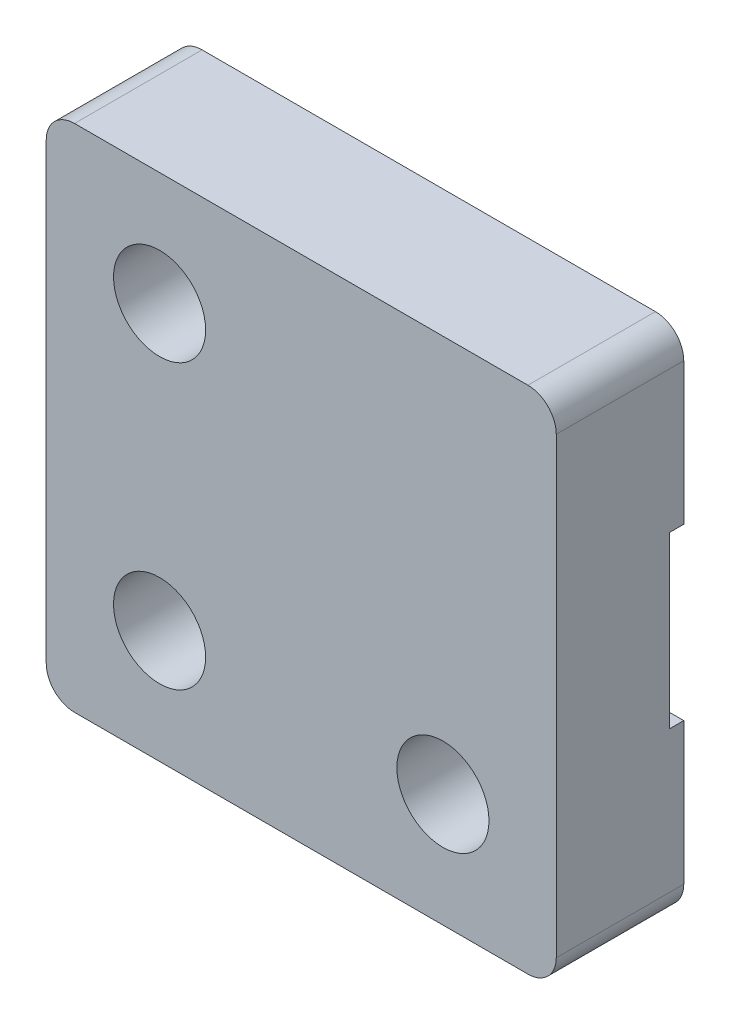
SolidWorks part; units mm, degrees
ref_plane "Front Plane" through (0, 0, 0) normal (0, 0, 1) x (1, 0, 0)
ref_plane "Top Plane" through (0, 0, 0) normal (0, 1, 0) x (1, 0, 0)
ref_plane "Right Plane" through (0, 0, 0) normal (1, 0, 0) x (0, 0, -1)
sketch "Sketch1" plane through (0, 0, 0) normal (0, 0, 1) x (1, 0, 0)
  line L0 (14, 14) -> (14, 4) construction
  line L1 (0, 0) -> (18, 0)
  line L2 (0, 0) -> (0, 18)
  line L3 (0, 18) -> (18, 18)
  line L4 (18, 0) -> (18, 18)
  line L5 (14, 4) -> (4, 4) construction
  circle A0 centre (4, 4) radius 1.625
  circle A1 centre (14, 4) radius 1.625
  circle A2 centre (14, 14) radius 1.625
  dimension "D1" = 3.25
  dimension "D2" = 18
  dimension "D3" = 10
  dimension "D4" = 4
  dimension "D5" = 4
extrude "Boss-Extrude1" add sketch "Sketch1" along normal blind 4
sketch "Sketch2" plane through (0, 0, 0) normal (0, 0, -1) x (-1, 0, 0)
  line L0 (-18, 0) -> (-18, 18) construction
  line L1 (-18, 12) -> (-17, 12)
  line L2 (-18, 12) -> (-18, 6)
  line L3 (-18, 6) -> (-17, 6)
  line L4 (-17, 12) -> (-17, 6)
  line L5 (-16, 12) -> (-16, 6)
  line L6 (-17, 12) -> (-16, 12)
  line L7 (-17, 12) -> (-17, 6)
  line L8 (-17, 6) -> (-16, 6)
  line L9 (-15, 12) -> (-15, 6)
  line L10 (-16, 12) -> (-15, 12)
  line L11 (-16, 12) -> (-16, 6)
  line L12 (-16, 6) -> (-15, 6)
  line L13 (-14, 12) -> (-14, 6)
  line L14 (-15, 12) -> (-14, 12)
  line L15 (-15, 12) -> (-15, 6)
  line L16 (-15, 6) -> (-14, 6)
  line L17 (-13, 12) -> (-13, 6)
  line L18 (-14, 12) -> (-13, 12)
  line L19 (-14, 12) -> (-14, 6)
  line L20 (-14, 6) -> (-13, 6)
  line L21 (-12, 12) -> (-12, 6)
  line L22 (-13, 12) -> (-12, 12)
  line L23 (-13, 12) -> (-13, 6)
  line L24 (-13, 6) -> (-12, 6)
  line L25 (-11, 12) -> (-11, 6)
  line L26 (-12, 12) -> (-11, 12)
  line L27 (-12, 12) -> (-12, 6)
  line L28 (-12, 6) -> (-11, 6)
  line L29 (-10, 12) -> (-10, 6)
  line L30 (-11, 12) -> (-10, 12)
  line L31 (-11, 12) -> (-11, 6)
  line L32 (-11, 6) -> (-10, 6)
  line L33 (-9, 12) -> (-9, 6)
  line L34 (-10, 12) -> (-9, 12)
  line L35 (-10, 12) -> (-10, 6)
  line L36 (-10, 6) -> (-9, 6)
  line L37 (-8, 12) -> (-8, 6)
  line L38 (-9, 12) -> (-8, 12)
  line L39 (-9, 12) -> (-9, 6)
  line L40 (-9, 6) -> (-8, 6)
  line L41 (-7, 12) -> (-7, 6)
  line L42 (-8, 12) -> (-7, 12)
  line L43 (-8, 12) -> (-8, 6)
  line L44 (-8, 6) -> (-7, 6)
  line L45 (-6, 12) -> (-6, 6)
  line L46 (-7, 12) -> (-6, 12)
  line L47 (-7, 12) -> (-7, 6)
  line L48 (-7, 6) -> (-6, 6)
  line L49 (-5, 12) -> (-5, 6)
  line L50 (-6, 12) -> (-5, 12)
  line L51 (-6, 12) -> (-6, 6)
  line L52 (-6, 6) -> (-5, 6)
  line L53 (-4, 12) -> (-4, 6)
  line L54 (-5, 12) -> (-4, 12)
  line L55 (-5, 12) -> (-5, 6)
  line L56 (-5, 6) -> (-4, 6)
  line L57 (-3, 12) -> (-3, 6)
  line L58 (-4, 12) -> (-3, 12)
  line L59 (-4, 12) -> (-4, 6)
  line L60 (-4, 6) -> (-3, 6)
  line L61 (-2, 12) -> (-2, 6)
  line L62 (-3, 12) -> (-2, 12)
  line L63 (-3, 12) -> (-3, 6)
  line L64 (-3, 6) -> (-2, 6)
  line L65 (-1, 12) -> (-1, 6)
  line L66 (-2, 12) -> (-1, 12)
  line L67 (-2, 12) -> (-2, 6)
  line L68 (-2, 6) -> (-1, 6)
  line L69 (0, 12) -> (0, 6)
  line L70 (-1, 12) -> (0, 12)
  line L71 (-1, 12) -> (-1, 6)
  line L72 (-1, 6) -> (0, 6)
  line M7 (-18, 18) -> (-18, 0)
  dimension "D1" = 6
  dimension "D2" = 1
  dimension "D3" = 6
  dimension "D4" = 18
extrude "Cut-Extrude1" cut sketch "Sketch2" against normal blind 0.95 contours L4 L1 L3 M7 | L5 L12 L9 L10 | L13 L20 L17 L18 | L21 L28 L25 L26 | L29 L36 L33 L34 | L37 L44 L41 L42 | L45 L52 L49 L50 | L53 L60 L57 L58 | L61 L68 L65 L66
sketch "Sketch3" plane through (0, 0, 0) normal (0, 0, -1) x (-1, 0, 0)
  line L0 (0, 18) -> (0, 0) construction
  line L1 (-18, 18) -> (0, 18)
  line L2 (-18, 18) -> (-18, 12)
  line L3 (-18, 12) -> (0, 12)
  line L4 (-2, 12) -> (-2, 6)
  line L5 (-1, 12) -> (-2, 12)
  line L6 (-1, 6) -> (-1, 12)
  line L7 (-2, 6) -> (-1, 6)
  line L8 (-2, 12) -> (-2, 6)
  line L9 (-1, 12) -> (-2, 12)
  line L10 (-1, 6) -> (-1, 12)
  line L11 (-2, 6) -> (-1, 6)
  line L12 (-4, 12) -> (-4, 6)
  line L13 (-3, 12) -> (-4, 12)
  line L14 (-3, 6) -> (-3, 12)
  line L15 (-4, 6) -> (-3, 6)
  line L16 (-4, 12) -> (-4, 6)
  line L17 (-3, 12) -> (-4, 12)
  line L18 (-3, 6) -> (-3, 12)
  line L19 (-4, 6) -> (-3, 6)
  line L20 (-6, 12) -> (-6, 6)
  line L21 (-5, 12) -> (-6, 12)
  line L22 (-5, 6) -> (-5, 12)
  line L23 (-6, 6) -> (-5, 6)
  line L24 (-6, 12) -> (-6, 6)
  line L25 (-5, 12) -> (-6, 12)
  line L26 (-5, 6) -> (-5, 12)
  line L27 (-6, 6) -> (-5, 6)
  line L28 (-8, 12) -> (-8, 6)
  line L29 (-7, 12) -> (-8, 12)
  line L30 (-7, 6) -> (-7, 12)
  line L31 (-8, 6) -> (-7, 6)
  line L32 (-8, 12) -> (-8, 6)
  line L33 (-7, 12) -> (-8, 12)
  line L34 (-7, 6) -> (-7, 12)
  line L35 (-8, 6) -> (-7, 6)
  line L36 (-10, 12) -> (-10, 6)
  line L37 (-9, 12) -> (-10, 12)
  line L38 (-9, 6) -> (-9, 12)
  line L39 (-10, 6) -> (-9, 6)
  line L40 (-10, 12) -> (-10, 6)
  line L41 (-9, 12) -> (-10, 12)
  line L42 (-9, 6) -> (-9, 12)
  line L43 (-10, 6) -> (-9, 6)
  line L44 (-12, 12) -> (-12, 6)
  line L45 (-11, 12) -> (-12, 12)
  line L46 (-11, 6) -> (-11, 12)
  line L47 (-12, 6) -> (-11, 6)
  line L48 (-12, 12) -> (-12, 6)
  line L49 (-11, 12) -> (-12, 12)
  line L50 (-11, 6) -> (-11, 12)
  line L51 (-12, 6) -> (-11, 6)
  line L52 (-14, 12) -> (-14, 6)
  line L53 (-13, 12) -> (-14, 12)
  line L54 (-13, 6) -> (-13, 12)
  line L55 (-14, 6) -> (-13, 6)
  line L56 (-14, 12) -> (-14, 6)
  line L57 (-13, 12) -> (-14, 12)
  line L58 (-13, 6) -> (-13, 12)
  line L59 (-14, 6) -> (-13, 6)
  line L60 (-16, 12) -> (-16, 6)
  line L61 (-15, 12) -> (-16, 12)
  line L62 (-15, 6) -> (-15, 12)
  line L63 (-16, 6) -> (-15, 6)
  line L64 (-16, 12) -> (-16, 6)
  line L65 (-15, 12) -> (-16, 12)
  line L66 (-15, 6) -> (-15, 12)
  line L67 (-16, 6) -> (-15, 6)
  line L68 (0, 18) -> (0, 12)
  line L70 (-18, 6) -> (0, 6)
  line L71 (-18, 6) -> (-18, 0)
  line L72 (-18, 0) -> (0, 0)
  line L73 (0, 6) -> (0, 0)
  circle A1 centre (-4, 4) radius 1.625
  circle A2 centre (-4, 4) radius 1.625
  circle A3 centre (-14, 4) radius 1.625
  circle A4 centre (-14, 4) radius 1.625
  circle A5 centre (-14, 14) radius 1.625
  circle A6 centre (-14, 14) radius 1.625
  line M36 (-17, 6) -> (-18, 6)
  line M37 (-18, 6) -> (-18, 0)
  line M38 (-18, 0) -> (0, 0)
  line M39 (0, 0) -> (0, 18)
  line M40 (0, 18) -> (-18, 18)
  line M41 (-18, 18) -> (-18, 12)
  line M42 (-18, 12) -> (-17, 12)
  line M45 (-16, 12) -> (-15, 12)
  line M47 (-15, 6) -> (-16, 6)
  line M49 (-14, 12) -> (-13, 12)
  line M51 (-13, 6) -> (-14, 6)
  line M53 (-12, 12) -> (-11, 12)
  line M55 (-11, 6) -> (-12, 6)
  line M57 (-10, 12) -> (-9, 12)
  line M59 (-9, 6) -> (-10, 6)
  line M61 (-8, 12) -> (-7, 12)
  line M63 (-7, 6) -> (-8, 6)
  line M65 (-6, 12) -> (-5, 12)
  line M67 (-5, 6) -> (-6, 6)
  line M69 (-4, 12) -> (-3, 12)
  line M71 (-3, 6) -> (-4, 6)
  line M73 (-2, 12) -> (-1, 12)
  line M75 (-1, 6) -> (-2, 6)
  circle M76 centre (-14, 4) radius 1.625
  circle M77 centre (-4, 4) radius 1.625
  circle M78 centre (-14, 14) radius 1.625
  dimension "D1" = 0
  dimension "D2" = 0
  dimension "D3" = 0
  dimension "D4" = 0
  dimension "D5" = 0
  dimension "D6" = 0
  dimension "D7" = 0
  dimension "D8" = 0
  dimension "D9" = 0
  dimension "D10" = 0
  dimension "D11" = 0
extrude "Boss-Extrude2" add sketch "Sketch3" along normal blind 0.5 contours L70 M36 M37 M38 M39 M75 M71 M67 M63 M59 M55 M51 M47 M76 M77 | L3 M42 M45 M49 M53 M57 M61 M65 M69 M73 M39 M40 M41 M78
fillet "Fillet1" radius 1 4 edges at (0, 0, 1.75) (18, 0, 1.75) (18, 18, 1.75) (0, 18, 1.75)
mirror "Mirror1" about plane through (18, 0, 4) normal (-1, 0, 0) of bodies 103
delete or keep bodies "Body-Delete/Keep 1" type delete bodies bodies 103
